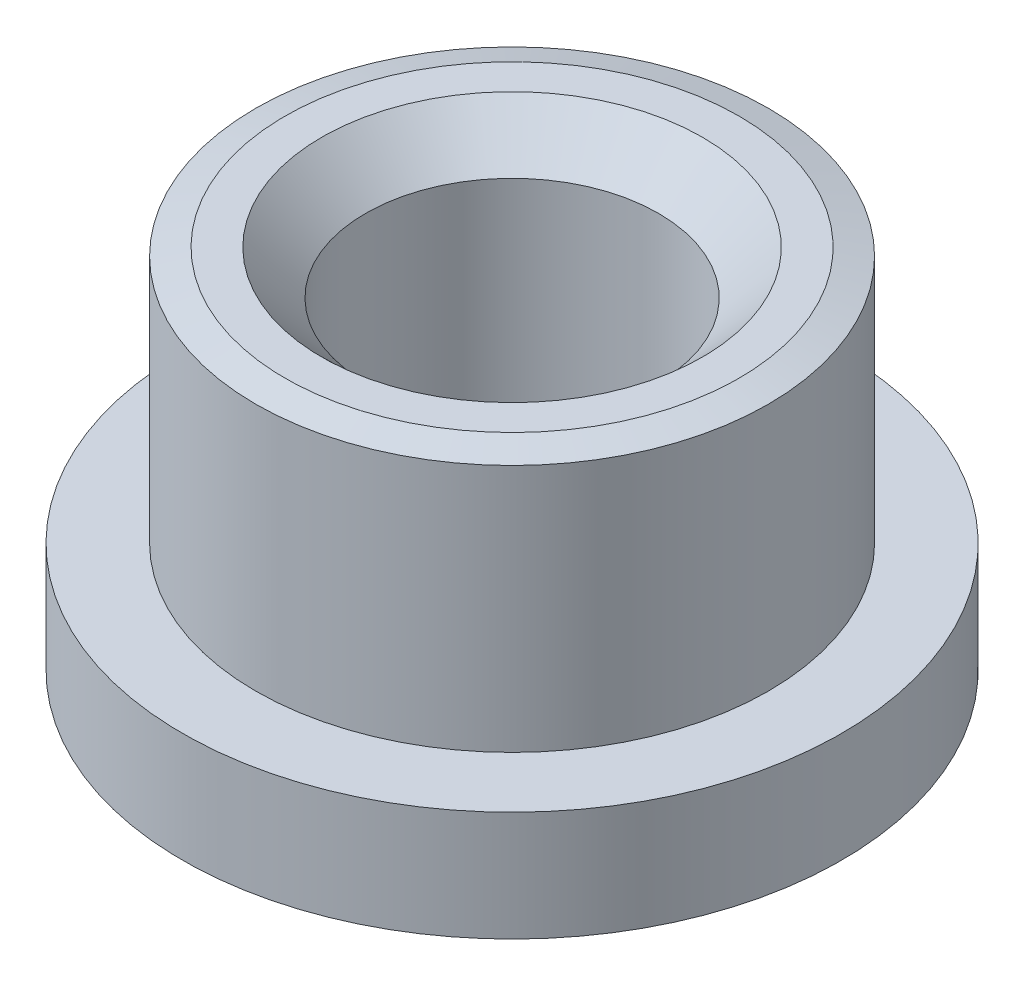
SolidWorks part; units mm, degrees
material "Литая легированная сталь"
ref_plane "Спереди" through (0, 0, 0) normal (0, 0, 1) x (1, 0, 0)
ref_plane "Сверху" through (0, 0, 0) normal (0, 1, 0) x (1, 0, 0)
ref_plane "Справа" through (0, 0, 0) normal (1, 0, 0) x (0, 0, -1)
sketch "Эскиз3" plane through (0, 0, 0) normal (0, 0, 1) x (1, 0, 0)
  line L0 (-4, 0) -> (-9, 0)
  line L1 (-9, 0) -> (-9, 3)
  line L2 (-9, 3) -> (-7, 3)
  line L3 (-7, 3) -> (-7, 10)
  line L4 (-7, 10) -> (-4, 10)
  line L5 (-4, 10) -> (-4, 0)
  line L6 (0, -11.6876) -> (0, 11.6876) construction
  point P10 (0, 0)
  dimension "D1" = 4
  dimension "D2" = 5
  dimension "D3" = 10
  dimension "D4" = 7
  dimension "D5" = 3
revolve "Повернуть1" add sketch "Эскиз3" angle 360 about L6
chamfer "Фаска1" distance 0.8 angle 15 1 edges at (0, 10, -7)
chamfer "Фаска2" distance 1.2 angle 45 1 edges at (0, 10, -4)
